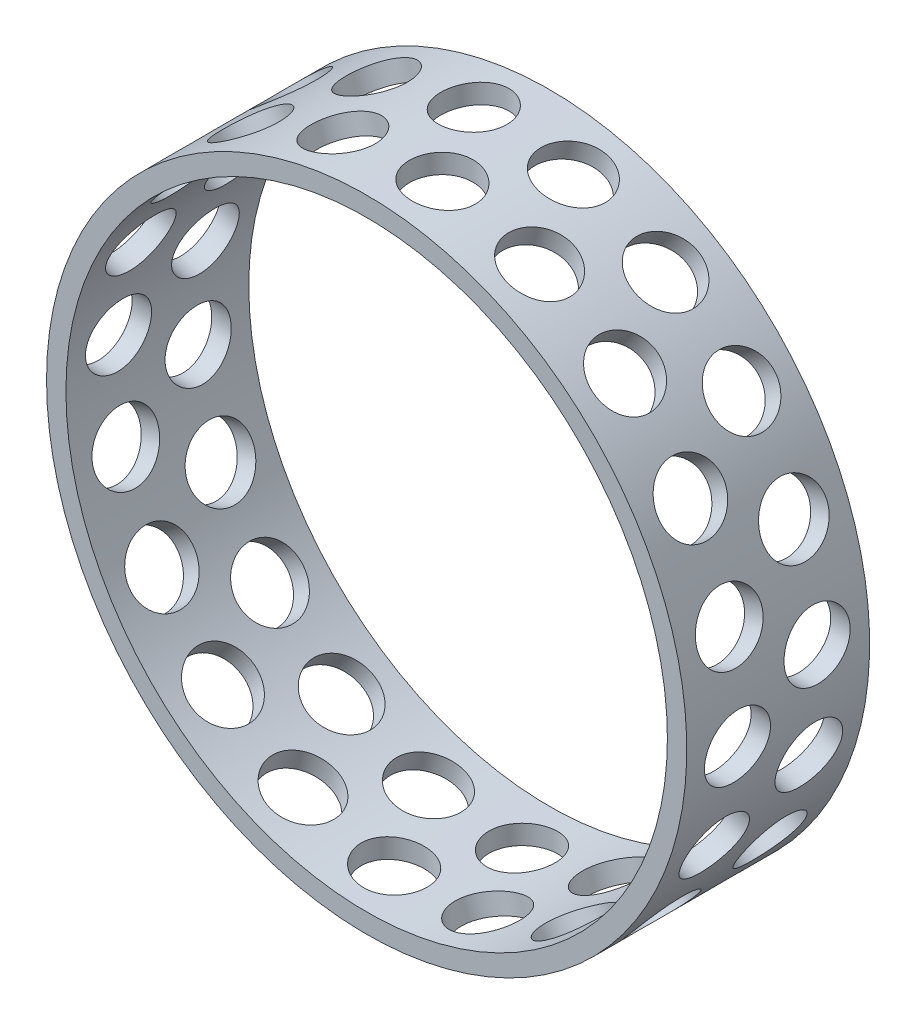
SolidWorks part; units mm, degrees
material "6061-T6 (SS)"
ref_plane "Front Plane" through (0, 0, 0) normal (0, 0, 1) x (1, 0, 0)
ref_plane "Top Plane" through (0, 0, 0) normal (0, 1, 0) x (1, 0, 0)
ref_plane "Right Plane" through (0, 0, 0) normal (1, 0, 0) x (0, 0, -1)
sketch "Sketch1" plane through (0, 0, 0) normal (1, 0, 0) x (0, 0, -1)
  line L0 (1, 82.55) -> (48.15, 82.55)
  line L1 (48.15, 82.55) -> (48.15, 77.55)
  line L2 (48.15, 77.55) -> (1, 77.55)
  line L3 (1, 77.55) -> (1, 82.55)
  dimension "D1" = 82.55
  dimension "D2" = 5
  dimension "D3" = 47.15
  dimension "D4" = 1
ref_axis "Axis1" through (0, 0, -50.5075) along (0, 0, 1)
revolve "Revolve1" add sketch "Sketch1" angle 360 about axis through (0, 0, -50.5075) along (0, 0, 1)
sketch "Sketch2" plane through (0, 0, 0) normal (1, 0, 0) x (0, 0, -1)
  line L0 (14.3098, 6.2149) -> (24.575, 0) construction
  line L1 (50.5075, 0) -> (-1.3575, 0) construction
  line L2 (24.575, 0) -> (34.8402, -6.2149) construction
  line L3 (1, 82.55) -> (1, -82.55) construction
  circle A0 centre (14.3098, 6.2149) radius 8.5
  circle A1 centre (34.8402, -6.2149) radius 8.5
  dimension "D1" = 17
  dimension "D2" = 12
  dimension "D3" = 23.575
  dimension "D4" = 31.192
extrude "Cut-Extrude1" cut sketch "Sketch2" against normal through all
pattern_circular "CirPattern1" count 20 over 360 about axis through (0, 0, -50.5075) along (0, 0, 1) of "Cut-Extrude1"
equation "\"TubeDiameter\"= 6.500in"
equation "\"D1@Sketch1\"=\"TubeDiameter\"/2"
